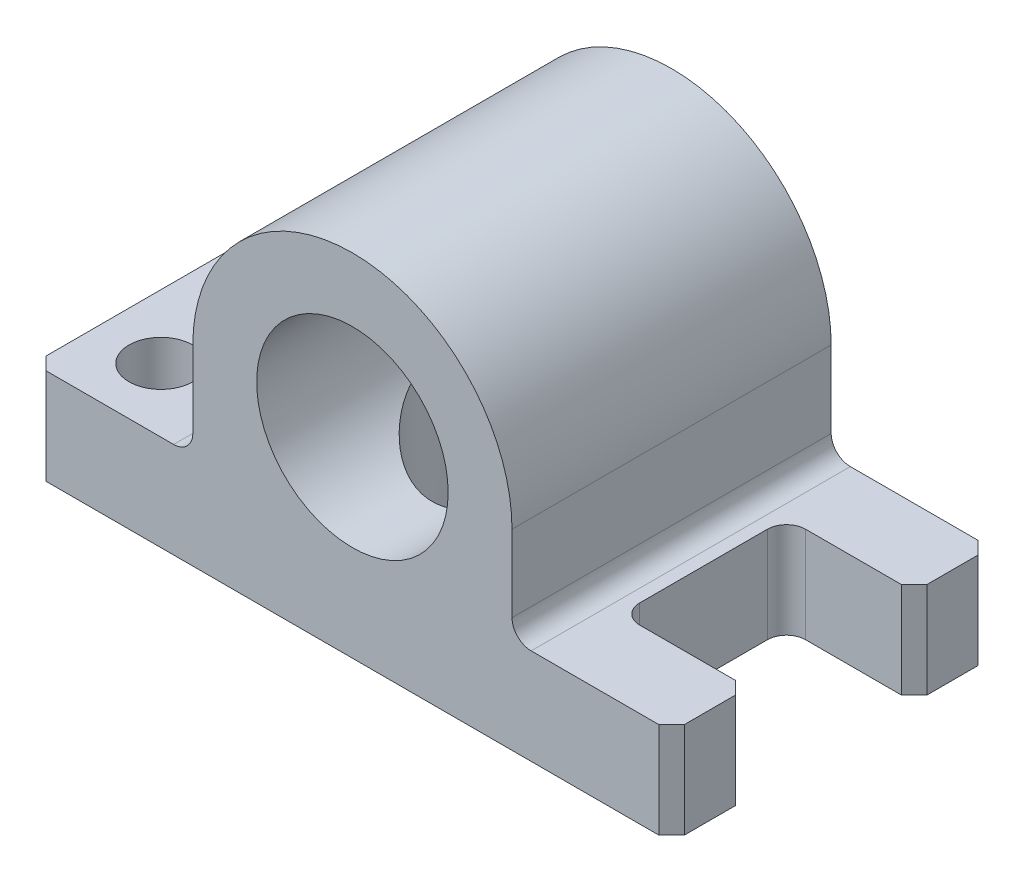
SolidWorks part; units mm, degrees
ref_plane "Front Plane" through (0, 0, 0) normal (0, 0, 1) x (1, 0, 0)
ref_plane "Top Plane" through (0, 0, 0) normal (0, 1, 0) x (1, 0, 0)
ref_plane "Right Plane" through (0, 0, 0) normal (1, 0, 0) x (0, 0, -1)
sketch "Sketch1" plane through (0, 0, 0) normal (0, 0, 1) x (1, 0, 0)
  line L0 (-50, -30) -> (50, -30)
  line L1 (50, -30) -> (50, -15)
  line L2 (50, -15) -> (25, -15)
  line L3 (25, -15) -> (25, 0)
  line L5 (-25, 0) -> (-25, -15)
  line L6 (-25, -15) -> (-50, -15)
  line L7 (-50, -15) -> (-50, -30)
  arc A0 (25, 0) -> (-25, 0) centre (0, 0) ccw
  circle A1 centre (0, 0) radius 15
  dimension "D4" = 30
  dimension "D5" = 25
  dimension "D1" = 100
  dimension "D2" = 15
  dimension "D3" = 15
extrude "Boss-Extrude2" add sketch "Sketch1" along normal mid plane 50
sketch "Sketch3" plane through (0, -30, 0) normal (0, -1, 0) x (1, 0, 0)
  line L0 (-50, 25) -> (-50, -25) construction
  circle A0 centre (0, 0) radius 12.5
  circle A1 centre (-40, 15) radius 5
  circle A2 centre (-40, -15) radius 5
  dimension "D1" = 10
  dimension "D2" = 10
  dimension "D5" = 10
  dimension "D6" = 25
  dimension "D3" = 15
  dimension "D4" = 30
extrude "Cut-Extrude1" cut sketch "Sketch3" against normal up to next
sketch "Sketch5" plane through (0, -30, 0) normal (0, -1, 0) x (1, 0, 0)
  line L0 (50, 25) -> (50, -25) construction
  line L1 (50, 13) -> (30, 13)
  line L2 (50, 13) -> (50, -13)
  line L3 (50, -13) -> (30, -13)
  line L4 (30, 13) -> (30, -13)
  point P6 (30, 0)
  dimension "D1" = 26
  dimension "D2" = 30
extrude "Cut-Extrude2" cut sketch "Sketch5" against normal up to next
fillet "Fillet2" radius 3 4 edges at (30, -22.5, -13) (30, -22.5, 13) (25, -15, 0) (-25, -15, 0)
chamfer "Chamfer1" distance 2 angle 45 6 edges at (-50, -22.5, 25) (-50, -22.5, -25) (50, -22.5, -25) (50, -22.5, -13) (50, -22.5, 13) (50, -22.5, 25)
